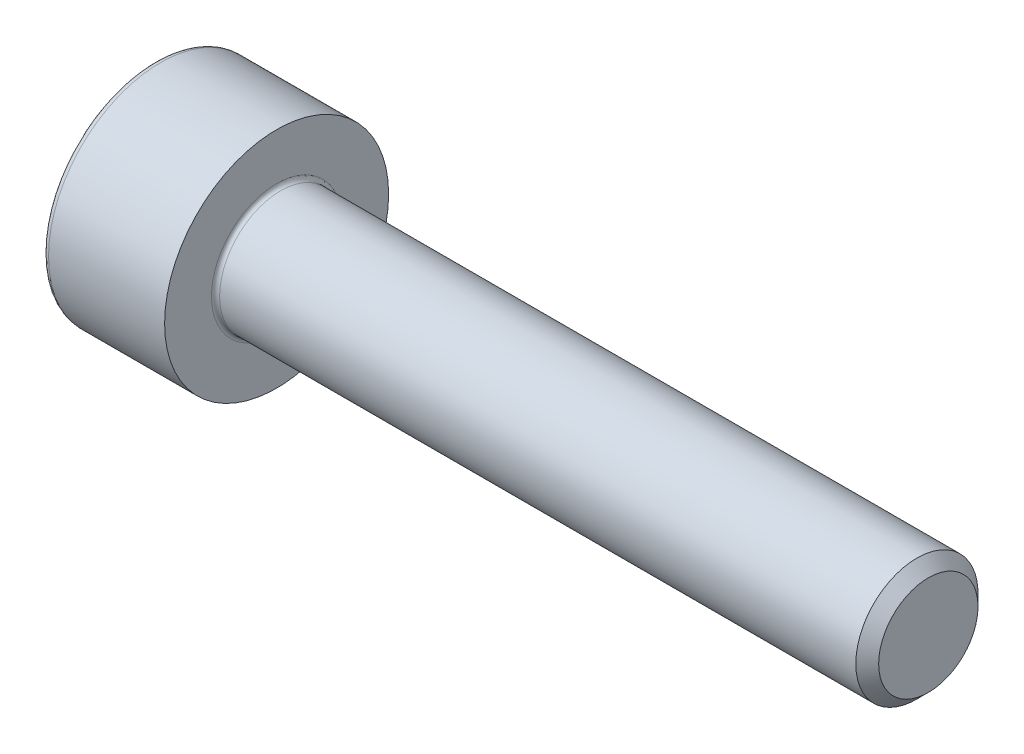
SolidWorks part; units mm, degrees
ref_plane "Plane1" through (0, 0, 0) normal (0, 0, 1) x (1, 0, 0)
ref_plane "Plane2" through (0, 0, 0) normal (0, 1, 0) x (1, 0, 0)
ref_plane "Plane3" through (0, 0, 0) normal (1, 0, 0) x (0, 0, -1)
sketch "BodySke" plane through (0, 0, 0) normal (0, 0, 1) x (1, 0, 0)
  line L0 (0, 0) -> (0, 2.75)
  line L1 (0, 2.75) -> (3, 2.75)
  line L2 (3, 2.75) -> (3, 1.5)
  line L3 (3, 1.5) -> (18.7195, 1.5)
  line L4 (19, 1.2195) -> (19, 0)
  line L5 (19, 0) -> (0, 0)
  line L6 (-31.75, 0) -> (127, 0) construction
  line L8 (19, 1.2195) -> (18.7195, 1.5)
  line L10 (19, -1.2195) -> (18.7195, -1.5) construction
  line L11 (3.5, 9.525) -> (3.5, 3.175) construction
  line L12 (3, 9.525) -> (3, 3.175) construction
  line L13 (-41, 9.525) -> (-41, 3.175) construction
  dimension "Diameter" = 3
  dimension "Head_ht" = 3
  dimension "Length" = 16
  dimension "Body_ch_ang" = 45
  dimension "Head_dia" = 5.5
  dimension "Minor_dia" = 2.439
  dimension "Advance" = 0.5
  dimension "Thread_nom" = 16
  dimension "Thread_length" = 60
revolve "Base-Revolve" add sketch "BodySke"
cosmetic thread "ThreadCosmetic"
fillet "Fillet1" radius 0.1 1 edges at (3, 0, 1.5)
fillet "Fillet2" radius 0.15 1 edges at (0, 0, 2.75)
sketch "Sketch2" plane through (0, 0, 0) normal (0, 0, 1) x (1, 0, 0)
  line L0 (0, 1.28) -> (1.3, 1.28)
  line L1 (1.3, 1.28) -> (2.039, 0)
  line L2 (-31.75, 0) -> (127, 0) construction
  line L3 (2.039, 0) -> (0, 0)
  line L4 (0, 0) -> (0, 1.28)
  line L6 (0, 0) -> (47.625, 0) construction
  dimension "D1" = 1.28
  dimension "D2" = 60
  dimension "Depth" = 1.3
revolve "Hex-PreBroach" cut sketch "Sketch2" angle 360 about L6
sketch "Sketch3" plane through (0, 0, 0) normal (-1, 0, 0) x (0, 0.5, 0.866)
  line L0 (0.739, 1.28) -> (-0.739, 1.28)
  line L1 (-0.739, 1.28) -> (-1.478, 0)
  line L2 (0.739, 1.28) -> (1.478, 0)
  line L3 (0.739, -1.28) -> (1.478, 0)
  line L4 (0.739, -1.28) -> (-0.739, -1.28)
  line L5 (-0.739, -1.28) -> (-1.478, 0)
  dimension "D1" = 1.28
  dimension "D2" = 1.28
  dimension "Hex_size" = 2.56
extrude "Hex" cut sketch "Sketch3" against normal blind 1.3
sketch "ThdSchSke" plane through (0, 0, 0) normal (0, 0, 1) x (1, 0, 0)
  line L0 (4.5, -1.2195) -> (4.3036, -1.5)
  line L1 (4.5, -1.2195) -> (4.6964, -1.5)
  line L2 (4.6964, -1.5) -> (4.6964, -1.875)
  line L3 (-3.175, 0) -> (5.1513, 0) construction
  line L4 (0, 2.6) -> (0, -2.6) construction
  line L5 (4.6964, -1.875) -> (4.3036, -1.875)
  line L6 (4.3036, -1.875) -> (4.3036, -1.5)
  dimension "Thread_minor" = 2.439
  dimension "Diameter" = 3
  dimension "Start" = 4.5
  dimension "SideAngle" = 55
  dimension "VeeAngle" = 70
  dimension "Overcut" = 3.75
revolve "ThreadSchematic" [suppressed] cut sketch "ThdSchSke" angle 360 about L3
pattern_linear "ThdSchPat" [suppressed]
equation "\"D2@Sketch3\" = \"Hex_size@Sketch3\" / 2"
equation "\"D1@Sketch3\" = \"Hex_size@Sketch3\" / 2"
equation "\"D1@Sketch2\" = \"Hex_size@Sketch3\" / 2"
equation "\"Thread_minor@ThreadCosmetic\"  =  \"Minor_dia@BodySke\""
equation "\"Depth@Sketch2\" =  \"Key_eng@Hex\""
equation "\"Thread_length@ThreadCosmetic\" = ((sgn( (\"Length@BodySke\" - \"Advance@BodySke\" * 3.0) - \"Thread_nom@BodySke\" )-1)*( (\"Length@BodySke\" - \"Advance@BodySke\" * 3.0) - \"Thread_nom@BodySke\" ))/-2+ \"Thread_nom@BodySke\""
equation "\"Thread_minor@ThdSchSke\" = \"Minor_dia@BodySke\""
equation "\"Diameter@ThdSchSke\" = \"Diameter@BodySke\""
equation "\"Overcut@ThdSchSke\" = \"Diameter@BodySke\" * 1.25"
equation "\"Start@ThdSchSke\" = \"Head_ht@BodySke\" + \"Length@BodySke\" - \"Thread_length@ThreadCosmetic\"  '---Non-countersunk---"
equation "\"Num_threads@ThdSchPat\" = int( \"Thread_length@ThreadCosmetic\" / \"Advance@BodySke\" + 0.999 )  + 1"
equation "\"Advance@ThdSchPat\" = \"Thread_length@ThreadCosmetic\" /  (\"Num_threads@ThdSchPat\" - 1) 'relax it"
equation "\"Num_threads@ThdSchPat\" = \"Num_threads@ThdSchPat\" - sgn( \"Num_threads@ThdSchPat\" - 1) '---chamfered tips only---"
